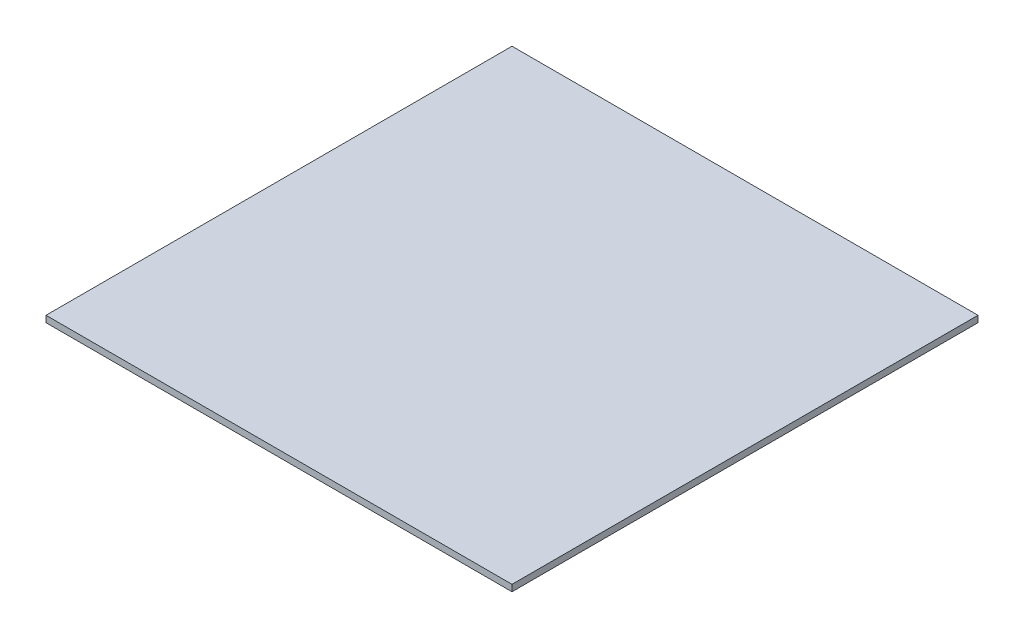
SolidWorks part; units mm, degrees
material "1060 Alloy"
ref_plane "Front Plane" through (0, 0, 0) normal (0, 0, 1) x (1, 0, 0)
ref_plane "Top Plane" through (0, 0, 0) normal (0, 1, 0) x (1, 0, 0)
ref_plane "Right Plane" through (0, 0, 0) normal (1, 0, 0) x (0, 0, -1)
sketch "Sketch1" plane through (0, 0, 0) normal (0, 1, 0) x (1, 0, 0)
  line L1 (-228.6, 228.6) -> (228.6, 228.6)
  line L2 (-228.6, 228.6) -> (-228.6, -228.6)
  line L3 (-228.6, -228.6) -> (228.6, -228.6)
  line L4 (228.6, 228.6) -> (228.6, -228.6)
  line L5 (-228.6, 228.6) -> (228.6, -228.6) construction
  line L6 (-228.6, -228.6) -> (228.6, 228.6) construction
  point P0 (0, 0)
  dimension "D1" = 457.2
  dimension "D2" = 457.2
extrude "Boss-Extrude1" add sketch "Sketch1" along normal blind 6.35
